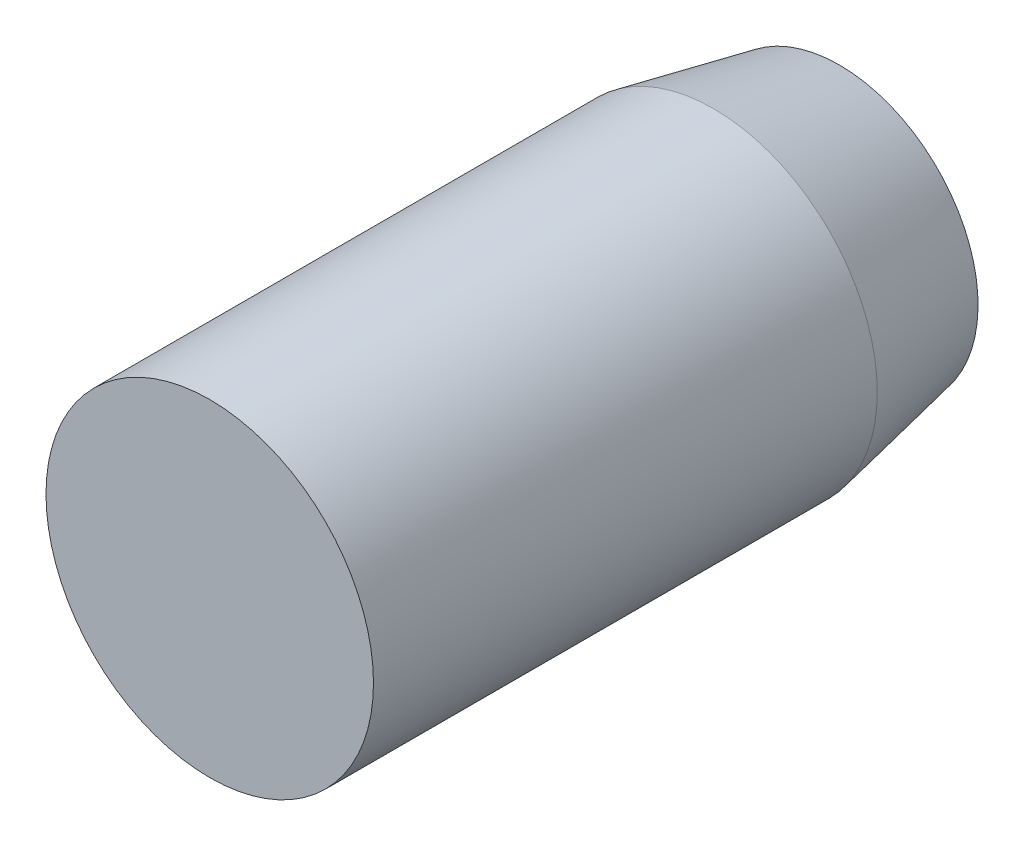
SolidWorks part; units mm, degrees
material "Plain Carbon Steel"
ref_plane "Front Plane" through (0, 0, 0) normal (0, 0, 1) x (1, 0, 0)
ref_plane "Top Plane" through (0, 0, 0) normal (0, 1, 0) x (1, 0, 0)
ref_plane "Right Plane" through (0, 0, 0) normal (1, 0, 0) x (0, 0, -1)
sketch "Sketch1" plane through (0, 0, 0) normal (1, 0, 0) x (0, 0, -1)
  line L0 (0, 0) -> (0, 6.5)
  line L1 (0, 6.5) -> (20, 6.5)
  line L2 (20, 6.5) -> (25, 5.5)
  line L3 (25, 5.5) -> (25, 0)
  line L4 (25, 0) -> (0, 0)
  dimension "D1" = 20
  dimension "D2" = 5.5
  dimension "D3" = 5
  dimension "D4" = 6.5
revolve "Revolve1" add sketch "Sketch1" angle 360 about L4
